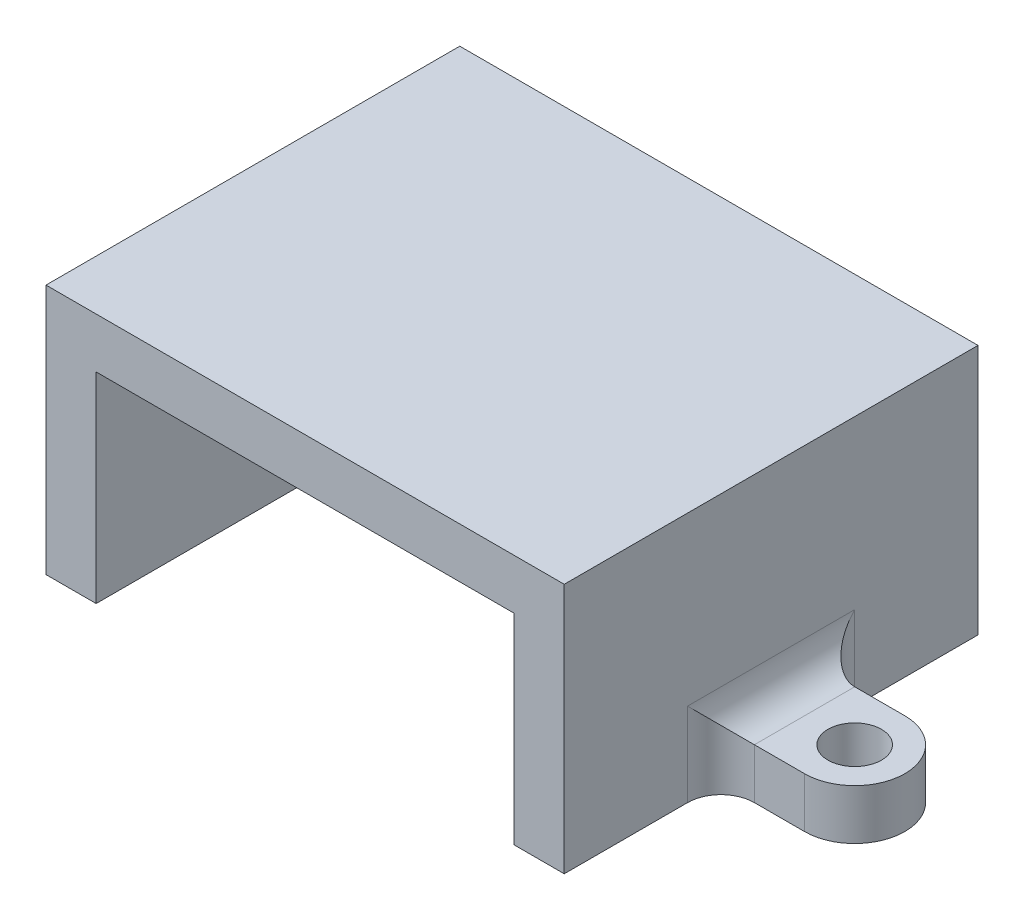
SolidWorks part; units mm, degrees
ref_plane "前视基准面" through (0, 0, 0) normal (0, 0, 1) x (1, 0, 0)
ref_plane "上视基准面" through (0, 0, 0) normal (0, 1, 0) x (1, 0, 0)
ref_plane "右视基准面" through (0, 0, 0) normal (1, 0, 0) x (0, 0, -1)
sketch "草图1" plane through (0, 0, 0) normal (0, 0, 1) x (1, 0, 0)
  line L0 (0, 0) -> (3, 0)
  line L1 (3, 0) -> (3, 12)
  line L2 (3, 12) -> (28, 12)
  line L3 (28, 12) -> (28, 0)
  line L4 (28, 0) -> (31, 0)
  line L5 (31, 0) -> (31, 15)
  line L6 (31, 15) -> (0, 15)
  line L7 (0, 15) -> (0, 0)
  dimension "D1" = 12
  dimension "D2" = 3
  dimension "D3" = 3
  dimension "D4" = 3
  dimension "D5" = 25
extrude "凸台-拉伸1" add sketch "草图1" along normal blind 24.75
sketch "草图2" plane through (0, 0, 0) normal (0, -1, 0) x (1, 0, 0)
  line L0 (15.5, 24.75) -> (15.5, -1.1402) construction
  line L1 (3, 24.75) -> (28, 24.75) construction
  line L2 (0, 12.375) -> (33.2336, 12.375) construction
  line L3 (0, 24.75) -> (0, 0) construction
  line L4 (36, 9.375) -> (31, 9.375)
  line L5 (31, 24.75) -> (31, 0) construction
  line L6 (31, 15.375) -> (31, 9.375)
  line L7 (0, 15.375) -> (0, 9.375)
  line L8 (-5, 9.375) -> (0, 9.375)
  line L9 (31, 15.375) -> (36, 15.375)
  line L10 (0, 15.375) -> (-5, 15.375)
  arc A0 (36, 9.375) -> (36, 15.375) centre (36, 12.375) ccw
  circle A1 centre (36, 12.375) radius 1.6
  circle A2 centre (-5, 12.375) radius 1.6
  arc A3 (-5, 9.375) -> (-5, 15.375) centre (-5, 12.375) cw
  dimension "D1" = 6
  dimension "D2" = 3.2
  dimension "D3" = 5
extrude "凸台-拉伸2" add sketch "草图2" against normal blind 3
fillet "圆角1" radius 2 6 edges at (0, 1.5, 15.375) (0, 1.5, 9.375) (0, 3, 12.375) (31, 1.5, 15.375) (31, 1.5, 9.375) (31, 3, 12.375)
